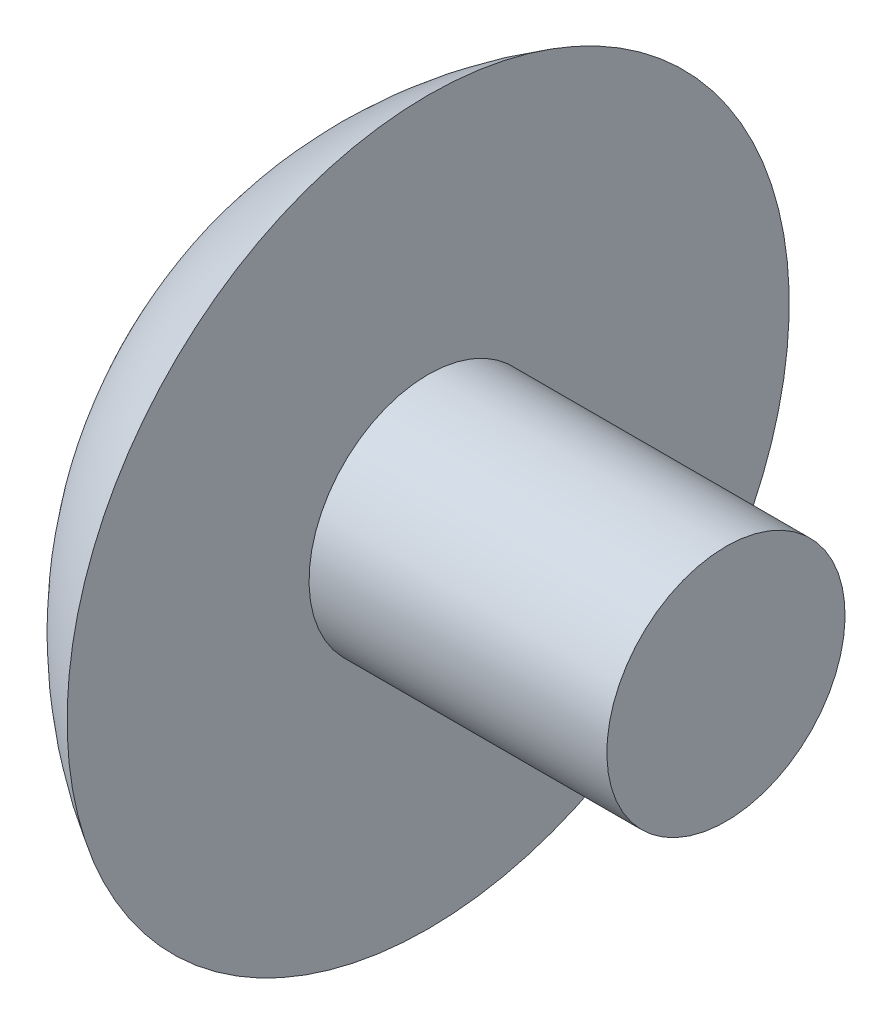
SolidWorks part; units mm, degrees
ref_plane "Plan de face" through (0, 0, 0) normal (0, 0, 1) x (1, 0, 0)
ref_plane "Plan de dessus" through (0, 0, 0) normal (0, 1, 0) x (1, 0, 0)
ref_plane "Plan de droite" through (0, 0, 0) normal (1, 0, 0) x (0, 0, -1)
sketch "Esquisse5" plane through (0, 0, 0) normal (0, 0, 1) x (1, 0, 0)
  line L0 (0, 0) -> (-8.5, 0)
  line L1 (0, 0) -> (0, -2)
  line L2 (0, -2) -> (-5, -2)
  line L3 (-5, -2) -> (-5, -6.0622)
  arc A0 (-8.5, 0) -> (-5, -6.0622) centre (-1.5, 0) ccw
  dimension "D1" = 7
  dimension "D2" = 8.5
  dimension "D3" = 2
  dimension "D4" = 5
revolve "Révolution2" add sketch "Esquisse5" angle 360 about L0
